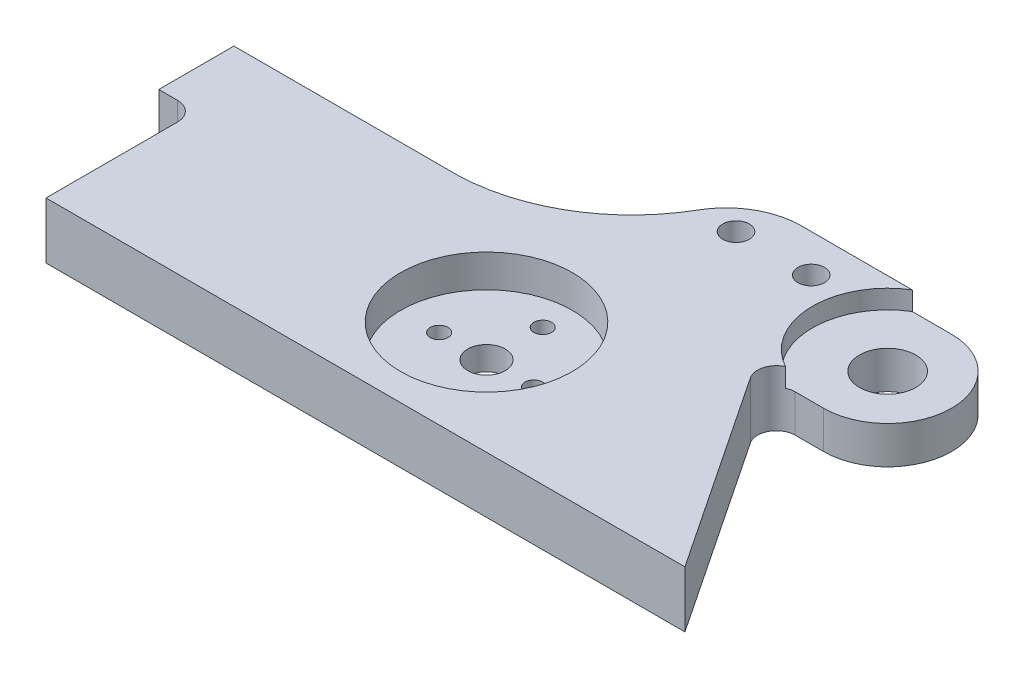
SolidWorks part; units mm, degrees
material "UHMW"
ref_plane "Front Plane" through (0, 0, 0) normal (0, 0, 1) x (1, 0, 0)
ref_plane "Top Plane" through (0, 0, 0) normal (0, 1, 0) x (1, 0, 0)
ref_plane "Right Plane" through (0, 0, 0) normal (1, 0, 0) x (0, 0, -1)
other "Bounding Box"
ref_plane "Default Plane" through (-8.9266, -12.7485, 0) normal (-0.1736, 0.9848, 0) x (0.9848, 0.1736, 0)
sketch "Sketch1" plane through (0, 0, 0) normal (0, 1, 0) x (1, 0, 0)
  line L0 (0, 0) -> (38.1, 0)
  line L1 (88.9, 0) -> (114.3, -38.1)
  line L2 (114.3, -38.1) -> (6.35, -38.1)
  line L3 (6.35, -38.1) -> (6.35, -12.7)
  line L4 (6.35, -12.7) -> (0, -12.7)
  line L5 (0, -12.7) -> (0, 0)
  line L6 (99.6289, 0) -> (88.9, 0)
  line L9 (99.6289, 21.632) -> (74.2289, 21.632)
  line L10 (61.7205, -19.05) -> (99.6289, 10.816) construction
  circle A0 centre (99.6289, 10.816) radius 4.7625
  arc A1 (99.6289, 21.632) -> (99.6289, 0) centre (99.6289, 10.816) cw
  arc A4 (74.2289, 21.632) -> (63.2185, 15.2614) centre (74.2289, 8.932) ccw
  arc A5 (63.2185, 15.2614) -> (38.1, 0) centre (36.7936, 30.452) cw
  circle A6 centre (69.5685, 15.2614) radius 2.2479
  circle A7 centre (82.2685, 15.2614) radius 2.2479
  circle B0 centre (69.7205, -19.05) radius 1.5
  circle B1 centre (61.7205, -28.55) radius 1.5
  circle B2 centre (53.7205, -19.05) radius 1.5
  circle B3 centre (61.7205, -9.55) radius 1.5
  circle B4 centre (61.7205, -19.05) radius 3.175
  dimension "D7" = 50.8
  dimension "D8" = 9.525
  dimension "D9" = 10.7289
  dimension "D6" = 10.816
  dimension "D10" = 30.48
  dimension "D16" = 12.7
  dimension "D19" = 4.4958
  dimension "D1" = 6.35
  dimension "D2" = 38.1
  dimension "D3" = 107.95
  dimension "D4" = 88.9
  dimension "D5" = 12.7
  dimension "D11" = 48.26
  dimension "D12" = 19.05
  dimension "D17" = 38.1
  dimension "D18" = 25.4
  dimension "D20" = 6.35
  dimension "D21" = 12.7
sketch_block_instance "Block1-1"
sketch_block "Block1" parameters "D1"=6.35
extrude "Boss-Extrude1" add sketch "Sketch1" along normal blind 9.525
fillet "Fillet1" radius 3.175 1 edges at (88.9, 4.7625, 0)
fillet "Fillet2" radius 3.175 1 edges at (6.35, 4.7625, 12.7)
sketch "Sketch2" plane through (0, 9.525, 0) normal (0, 1, 0) x (1, 0, 0)
  circle A0 centre (61.7205, -19.05) radius 14.5
  dimension "D1" = 29
extrude "Cut-Extrude1" cut sketch "Sketch2" against normal blind 5.525
sketch "Sketch3" plane through (0, 9.525, 0) normal (0, 1, 0) x (1, 0, 0)
  circle A4 centre (99.6289, 10.816) radius 12.7
  dimension "D1" = 25.4
extrude "Cut-Extrude2" cut sketch "Sketch3" against normal blind 3.175
